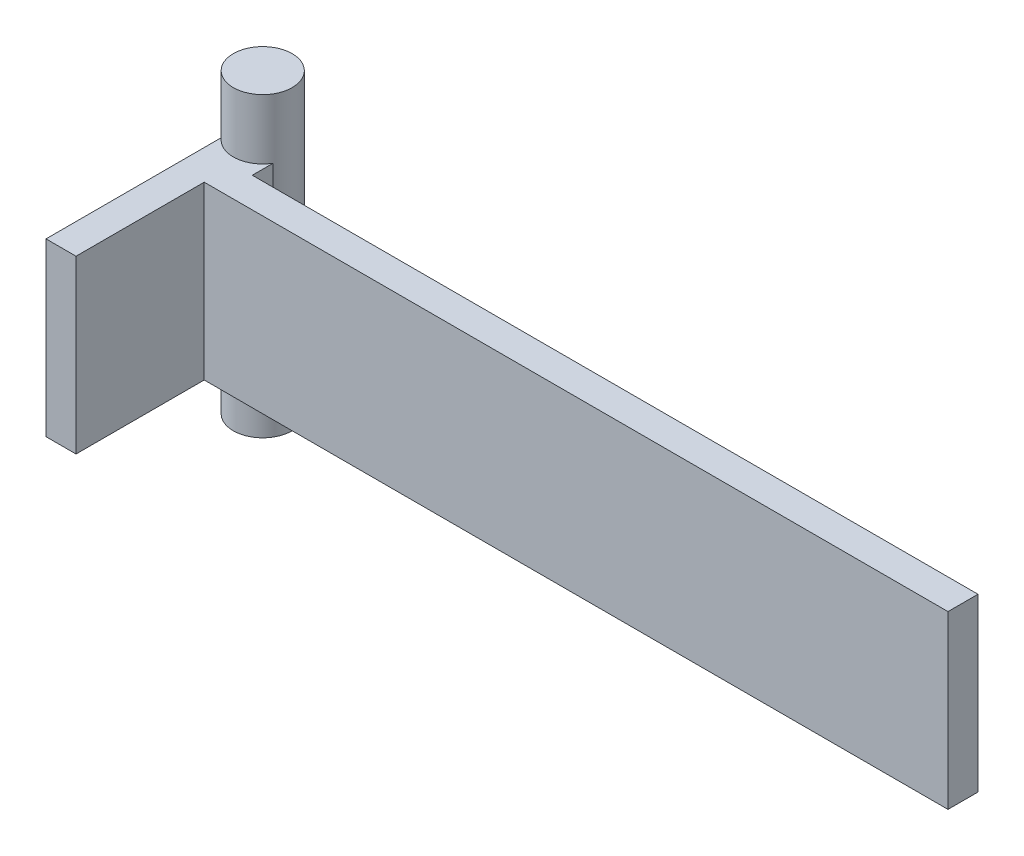
SolidWorks part; units mm, degrees
ref_plane "Front Plane" through (0, 0, 0) normal (0, 0, 1) x (1, 0, 0)
ref_plane "Top Plane" through (0, 0, 0) normal (0, 1, 0) x (1, 0, 0)
ref_plane "Right Plane" through (0, 0, 0) normal (1, 0, 0) x (0, 0, -1)
sketch "Sketch1" plane through (0, 0, 0) normal (0, 0, 1) x (1, 0, 0)
  line L0 (10, -1.47) -> (0, -1.47)
  line L1 (10, -1.47) -> (10, -30)
  line L2 (10, -30) -> (0, -30)
  line L3 (0, -1.47) -> (0, -30)
  dimension "D1" = 10
  dimension "D2" = 28.53
  dimension "D3" = 1.47
extrude "Boss-Extrude1" add sketch "Sketch1" along normal blind 5
sketch "Sketch2" plane through (0, 0, 0) normal (0, 0, -1) x (-1, 0, 0)
  line L0 (-10, -1.47) -> (0, -1.47) construction
  line L1 (-10, -30) -> (-10, -1.47) construction
  line L2 (0, -30) -> (-10, -30) construction
  circle A0 centre (-6.8103, -9.47) radius 1.6
  circle A1 centre (-6.8103, -22) radius 1.6
  dimension "D1" = 3.2
  dimension "D2" = 3.2
  dimension "D3" = 8
  dimension "D4" = 3.1897
  dimension "D5" = 8
  dimension "D6" = 3.1897
extrude "Cut-Extrude2" cut sketch "Sketch2" against normal blind 43
sketch "Sketch4" plane through (0, 0, 0) normal (0, 0, 1) x (1, 0, 0)
  line L0 (0, -30) -> (10, -30) construction
  line L1 (-5, -1.4695) -> (3, -1.4695)
  line L2 (-5, -1.4695) -> (-5, -30)
  line L3 (-5, -30) -> (3, -30)
  line L4 (3, -1.4695) -> (3, -30)
  line L5 (0, -1.47) -> (0, -30) construction
  dimension "D1" = 8
  dimension "D2" = 5
extrude "Boss-Extrude2" add sketch "Sketch4" against normal blind 5 and the other way up to surface (5 mm away)
ref_plane "Plane1" through (70.8497, 0, 0) normal (-1, 0, 0) x (0, 0, 1)
sketch "Sketch6" plane through (70.8497, 0, 0) normal (-1, 0, 0) x (0, 0, 1)
  line L0 (5, -1.4695) -> (-5, -1.4695) construction
  line L1 (5, -30) -> (0, -30)
  line L2 (5, -30) -> (5, -1.4695)
  line L3 (5, -1.4695) -> (0, -1.4695)
  line L4 (0, -30) -> (0, -1.4695)
  line L5 (5, -1.4695) -> (5, -30) construction
  line L6 (5, -30) -> (-5, -30) construction
  dimension "D1" = 5
extrude "Boss-Extrude4" add sketch "Sketch6" along normal up to surface and the other way up to surface
sketch "Sketch7" plane through (0, 0, 0) normal (0, 0, -1) x (-1, 0, 0)
  line L0 (0, -30) -> (0, -1.4695)
  line L1 (0, -30) -> (5, -30)
  line L2 (0, -1.4695) -> (5, -1.4695)
  line L3 (5, -30) -> (5, -1.4695)
  line L4 (-3, -30) -> (-123.8497, -30) construction
  line L5 (5, -1.4695) -> (-123.8497, -1.4695) construction
  dimension "D1" = 5
extrude "Boss-Extrude5" add sketch "Sketch7" against normal blind 26.35
sketch "Sketch8" plane through (0, -1.4695, 0) normal (0, 1, 0) x (1, 0, 0)
  line L0 (-5, -26.35) -> (0, -26.35)
  line L1 (-5, -26.35) -> (-5, -19.35)
  line L2 (0, -26.35) -> (0, -19.35)
  line L3 (-5, -19.35) -> (0, -19.35)
  line L4 (-5, -26.35) -> (-5, 5) construction
  line L5 (0, -26.35) -> (0, -5) construction
  line L6 (-5, -26.35) -> (0, -26.35) construction
  dimension "D1" = 7
extrude "Boss-Extrude6" add sketch "Sketch8" along normal up to surface (21.5043 mm away)
ref_plane "Plane2" through (0, -19.456, 0) normal (0, -1, 0) x (-1, 0, 0)
ref_plane "Plane4" through (0, -1.4695, 0) normal (0, 1, 0) x (1, 0, 0)
sketch "Sketch9" plane through (0, -1.4695, 0) normal (0, -1, 0) x (1, 0, 0)
  line L0 (-5, 26.35) -> (0, 26.35)
  line L1 (-5, 26.35) -> (-5, 5)
  line L2 (0, 26.35) -> (0, 5)
  line L3 (-5, 5) -> (0, 5)
  line L4 (-5, 26.35) -> (-5, -5) construction
  line L5 (0, 26.35) -> (0, 5) construction
  line L6 (0, 5) -> (123.8497, 5) construction
  line L7 (0, 26.35) -> (-5, 26.35) construction
  point P10 (-2.5, 26.35)
extrude "Cut-Extrude3" cut sketch "Sketch9" against normal through all
ref_plane "Plane3" through (0, -40.9652, 0) normal (0, -1, 0) x (-1, 0, 0)
sketch "Sketch10" plane through (0, -40.9652, 0) normal (0, -1, 0) x (1, 0, 0)
  circle A0 centre (-1.2141, -5.9555) radius 4.9
  dimension "D1" = 9.8
extrude "Boss-Extrude7" add sketch "Sketch10" against normal blind 49.5 separate body
